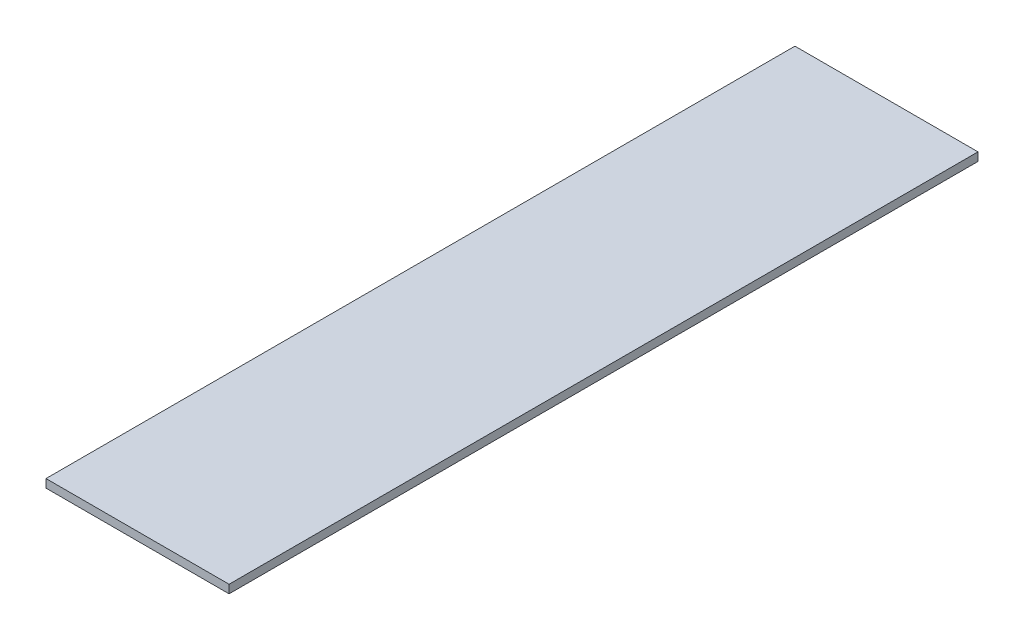
SolidWorks part; units mm, degrees
material "Balsa"
ref_plane "Front Plane" through (0, 0, 0) normal (0, 0, 1) x (1, 0, 0)
ref_plane "Top Plane" through (0, 0, 0) normal (0, 1, 0) x (1, 0, 0)
ref_plane "Right Plane" through (0, 0, 0) normal (1, 0, 0) x (0, 0, -1)
sketch "Sketch1" plane through (0, 0, 0) normal (0, 1, 0) x (1, 0, 0)
  line L0 (0, -225.5921) -> (0, 345.9079)
  line L1 (0, -225.5921) -> (-139.7, -225.5921)
  line L2 (0, 345.9079) -> (-139.7, 345.9079)
  line L3 (-139.7, -225.5921) -> (-139.7, 345.9079)
  dimension "D1" = 571.5
  dimension "D2" = 139.7
extrude "Boss-Extrude1" add sketch "Sketch1" against normal blind 6.35
